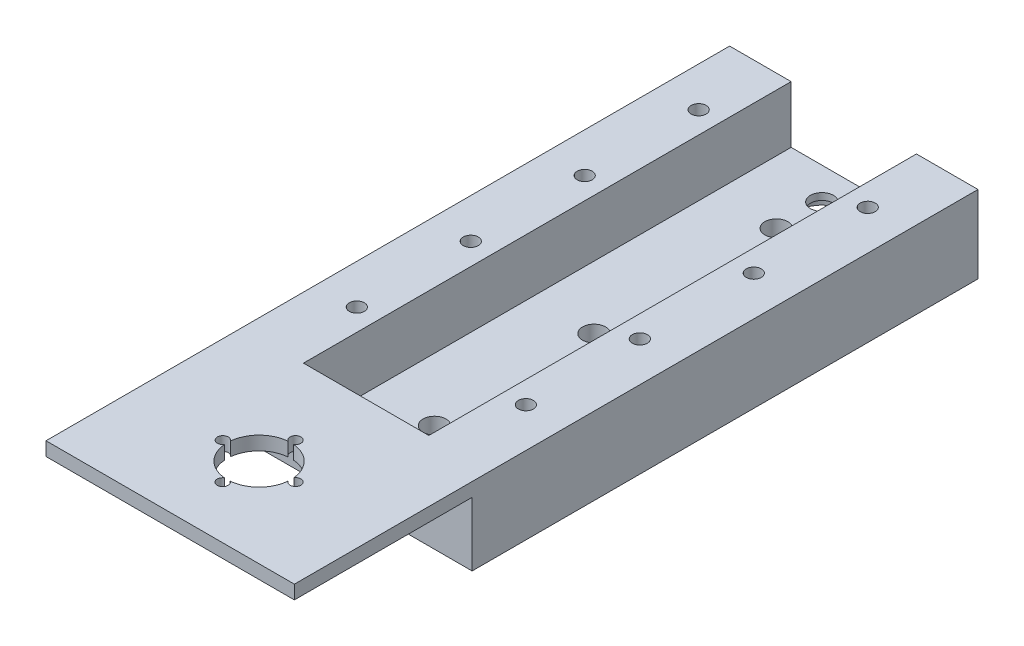
SolidWorks part; units mm, degrees
ref_plane "Front Plane" through (0, 0, 0) normal (0, 0, 1) x (1, 0, 0)
ref_plane "Top Plane" through (0, 0, 0) normal (0, 1, 0) x (1, 0, 0)
ref_plane "Right Plane" through (0, 0, 0) normal (1, 0, 0) x (0, 0, -1)
sketch "Sketch1" plane through (0, 0, 0) normal (0, 1, 0) x (1, 0, 0)
  line L1 (-40.6495, -11.3707) -> (13.8505, -11.3707)
  line L2 (-40.6495, -11.3707) -> (-40.6495, 99.6293)
  line L3 (-40.6495, 99.6293) -> (13.8505, 99.6293)
  line L4 (13.8505, -11.3707) -> (13.8505, 99.6293)
  dimension "D1" = 54.5
  dimension "D2" = 111
extrude "Boss-Extrude1" add sketch "Sketch1" along normal blind 4.5
sketch "Sketch2" plane through (0, 4.5, 0) normal (0, 1, 0) x (1, 0, 0)
  line L0 (13.8505, 99.6293) -> (-40.6495, 99.6293) construction
  line L1 (0.3505, 99.6293) -> (13.8505, 99.6293)
  line L2 (0.3505, 99.6293) -> (0.3505, -11.3707)
  line L3 (0.3505, -11.3707) -> (13.8505, -11.3707)
  line L4 (13.8505, 99.6293) -> (13.8505, -11.3707)
  line L5 (-40.6495, -11.3707) -> (13.8505, -11.3707) construction
  line L6 (-40.6495, 99.6293) -> (-27.1495, 99.6293)
  line L7 (-40.6495, 99.6293) -> (-40.6495, -11.3707)
  line L8 (-40.6495, -11.3707) -> (-27.1495, -11.3707)
  line L9 (-27.1495, 99.6293) -> (-27.1495, -11.3707)
  dimension "D1" = 13.5
  dimension "D2" = 13.5
extrude "Boss-Extrude2" add sketch "Sketch2" along normal blind 12.5 contours L7 L6 L9 L8 | L2 L1 L4 L3
hole_wizard "M4x0.7 Tapped Hole1" positions "3DSketch1" profile "Sketch3" tap size "M4x0.7" standard "ANSI Metric" end condition through all
sketch3d "3DSketch1"
  line L0 (-40.6495, 17, -99.6293) -> (-27.1495, 17, -99.6293) construction
  line L1 (-40.6495, 17, -99.6293) -> (-40.6495, 17, 11.3707) construction
  line L2 (-40.6495, 17, 11.3707) -> (-27.1495, 17, 11.3707) construction
  line L3 (0.3505, 17, -99.6293) -> (13.8505, 17, -99.6293) construction
  line L4 (13.8505, 17, -99.6293) -> (13.8505, 17, 11.3707) construction
  point P0 (-31.9495, 17, -9.1293)
  point P2 (-31.9495, 17, -34.1293)
  point P4 (-31.9495, 17, -59.1293)
  point P6 (-31.9495, 17, -84.1293)
  point P8 (5.1505, 17, -9.1293)
  point P10 (5.1505, 17, -34.1293)
  point P12 (5.1505, 17, -59.1293)
  point P14 (5.1505, 17, -84.1293)
  dimension "D1" = 15.5
  dimension "D2" = 8.7
  dimension "D3" = 25
  dimension "D4" = 8.7
  dimension "D5" = 25
  dimension "D6" = 8.7
  dimension "D7" = 25
  dimension "D8" = 8.7
  dimension "D9" = 20.5
  dimension "D10" = 15.5
  dimension "D11" = 8.7
  dimension "D12" = 25
  dimension "D13" = 8.7
  dimension "D14" = 25
  dimension "D15" = 8.7
  dimension "D16" = 8.7
  dimension "D17" = 25
sketch "Sketch3" plane through (-31.9495, 17, -9.1293) normal (1, 0, 0) x (0, 0, 1)
  line L0 (0, 0) -> (0, 17)
  line L1 (0, 17) -> (1.65, 17)
  line L2 (1.65, 17) -> (1.65, 0)
  line L5 (1.65, 0) -> (0, 0)
  line L11 (0, -6.35) -> (0, 107.95) construction
  dimension "Thru Tap Drill Dia." = 3.3
  dimension "Thru Tap Drill Depth" = 17
cosmetic thread "Hole Thread1" parameters "D2"=4
cosmetic thread "Hole Thread2" parameters "D2"=4
cosmetic thread "Hole Thread3" parameters "D2"=4
cosmetic thread "Hole Thread4" parameters "D2"=4
cosmetic thread "Hole Thread5" parameters "D2"=4
cosmetic thread "Hole Thread6" parameters "D2"=4
cosmetic thread "Hole Thread7" parameters "D2"=4
cosmetic thread "Hole Thread8" parameters "D2"=4
sketch "Sketch6" plane through (-27.1495, 0, 0) normal (1, 0, 0) x (0, 0, -1)
  line L0 (99.6293, 4.5) -> (-11.3707, 4.5) construction
  line L1 (-11.3707, 17) -> (-7.3707, 17)
  line L2 (-11.3707, 17) -> (-11.3707, 4.5)
  line L3 (-11.3707, 4.5) -> (-7.3707, 4.5)
  line L4 (-7.3707, 17) -> (-7.3707, 4.5)
  dimension "D1" = 4
extrude "Boss-Extrude3" add sketch "Sketch6" along normal blind 37
sketch "Sketch7" plane through (0, 0, 11.3707) normal (0, 0, 1) x (1, 0, 0)
  line L0 (13.8505, 17) -> (13.8505, 0) construction
  line L1 (-40.6495, 17) -> (13.8505, 17)
  line L2 (-40.6495, 17) -> (-40.6495, 14)
  line L3 (-40.6495, 14) -> (13.8505, 14)
  line L4 (13.8505, 17) -> (13.8505, 14)
  dimension "D1" = 3
extrude "Boss-Extrude5" add sketch "Sketch7" along normal blind 39
sketch "Sketch8" plane through (0, 17, 0) normal (0, 1, 0) x (1, 0, 0)
  line L1 (-40.6495, 99.6293) -> (-40.6495, -50.3707) construction
  circle A0 centre (-13.3995, -30.8707) radius 7
  dimension "D1" = 19.5
  dimension "D2" = 27.25
extrude "Cut-Extrude1" cut sketch "Sketch8" against normal blind 3 contours A0
hole_wizard "M2 Clearance Hole1" positions "3DSketch2" profile "Sketch9" hole size "M2" standard "ANSI Metric" end condition through all
sketch3d "3DSketch2"
  line L0 (13.8505, 17, 50.3707) -> (-40.6495, 17, 50.3707) construction
  line L1 (13.8505, 17, -99.6293) -> (13.8505, 17, 50.3707) construction
  point P0 (-21.3714, 17, 30.8479)
  point P2 (-13.3995, 17, 22.8707)
  point P4 (-13.3995, 17, 38.8707)
  point P12 (-5.4305, 17, 30.8451)
  dimension "D1" = 11.5
  dimension "D2" = 16
  dimension "D3" = 27.25
  dimension "D4" = 27.25
  dimension "D5" = 11.31
  dimension "D6" = 11.31
sketch "Sketch9" plane through (-21.3714, 17, 30.8479) normal (1, 0, 0) x (0, 0, 1)
  line L0 (0, 0) -> (0, 17)
  line L1 (0, 17) -> (1.2, 17)
  line L2 (1.2, 17) -> (1.2, 0)
  line L5 (1.2, 0) -> (0, 0)
  line L11 (0, -6.35) -> (0, 107.95) construction
  dimension "Thru Hole Dia." = 2.4
  dimension "Thru Hole Depth" = 17
hole_wizard "#8 (0.199) Diameter Hole1" positions "3DSketch4" profile "Sketch10" hole size "#8" standard "Progressive" end condition through all
sketch3d "3DSketch4"
  line L4 (0.3505, 4.5, -99.6293) -> (0.3505, 4.5, 7.3707) construction
  line L6 (0.3505, 4.5, 7.3707) -> (-27.1495, 4.5, 7.3707) construction
  line L7 (0.3505, 4.5, -99.6293) -> (-27.1495, 4.5, -99.6293) construction
  point P0 (-13.3995, 4.5, 2.3707)
  point P2 (-13.3995, 4.5, -7.6293)
  point P4 (-13.3995, 4.5, -42.6293)
  point P6 (-13.3995, 4.5, -82.6293)
  point P8 (-13.3995, 4.5, -92.6293)
  dimension "D1" = 13.75
  dimension "D2" = 13.75
  dimension "D4" = 13.75
  dimension "D3" = 13.75
  dimension "D5" = 13.75
  dimension "D6" = 5
  dimension "10" = 10
  dimension "D7" = 7
  dimension "D8" = 10
  dimension "D9" = 35
sketch "Sketch10" plane through (-13.3995, 4.5, 2.3707) normal (1, 0, 0) x (0, 0, 1)
  line L0 (0, 0) -> (0, 4.5)
  line L1 (0, 4.5) -> (2.5273, 4.5)
  line L2 (2.5273, 4.5) -> (2.5273, 0)
  line L5 (2.5273, 0) -> (0, 0)
  line L11 (0, -6.35) -> (0, 107.95) construction
  dimension "Thru Hole Dia." = 5.0546
  dimension "Thru Hole Depth" = 4.5
sketch "Sketch12" plane through (0, 0, 0) normal (0, -1, 0) x (-1, 0, 0)
  circle A2 centre (13.3995, 92.6293) radius 5.5
extrude "Cut-Extrude3" cut sketch "Sketch12" against normal blind 3
